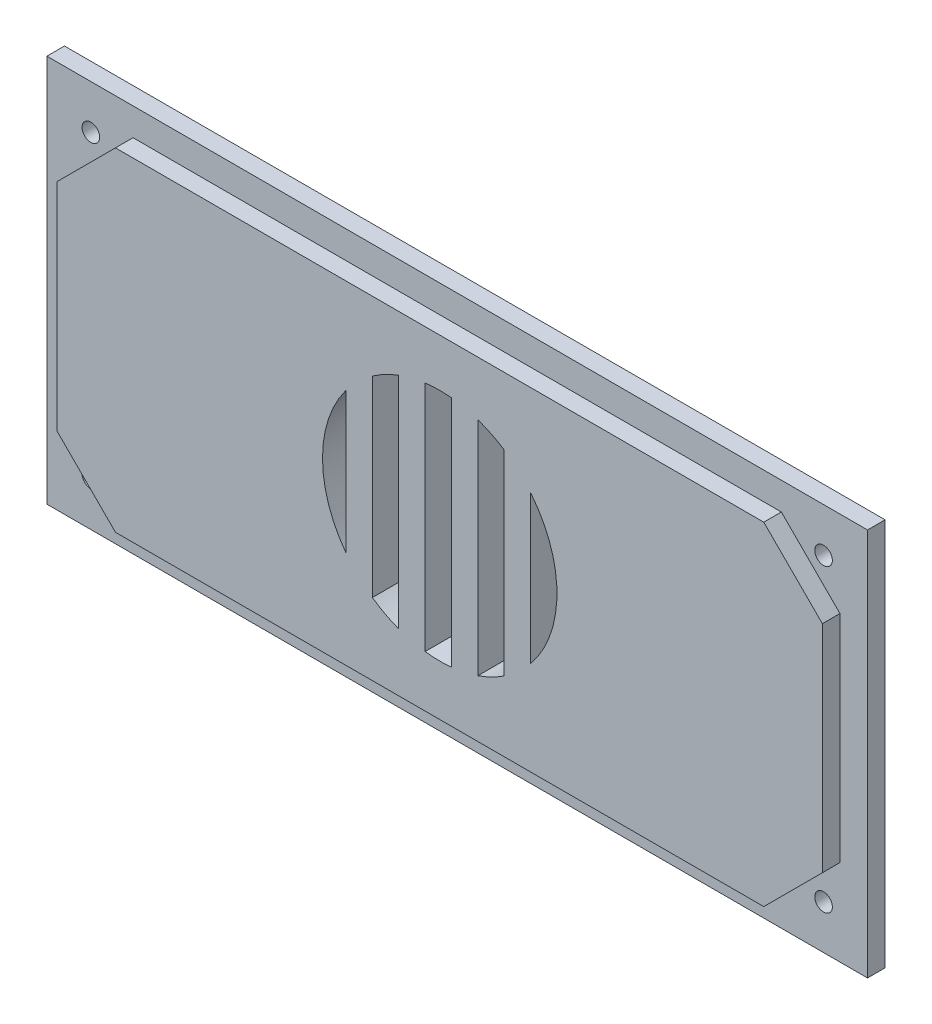
SolidWorks part; units mm, degrees
ref_plane "Front Plane" through (0, 0, 0) normal (0, 0, 1) x (1, 0, 0)
ref_plane "Top Plane" through (0, 0, 0) normal (0, 1, 0) x (1, 0, 0)
ref_plane "Right Plane" through (0, 0, 0) normal (1, 0, 0) x (0, 0, -1)
sketch "Sketch2" plane through (0, 0, 0) normal (0, 0, 1) x (1, 0, 0)
  line L1 (-70, 33.1) -> (70, 33.1)
  line L2 (-70, 33.1) -> (-70, -33.1)
  line L3 (-70, -33.1) -> (70, -33.1)
  line L4 (70, 33.1) -> (70, -33.1)
  line L5 (0, -33.1) -> (0, 33.1) construction
  line L6 (-70, 0) -> (70, 0) construction
  point P0 (0, 0)
  dimension "D1" = 140
  dimension "D2" = 66.2
extrude "Boss-Extrude1" add sketch "Sketch2" against normal blind 3
sketch "Sketch3" plane through (0, 0, 0) normal (0, 0, 1) x (1, 0, 0)
  line L1 (-65.3, 28.4) -> (65.3, 28.4)
  line L2 (-65.3, 28.4) -> (-65.3, -28.4)
  line L3 (-65.3, -28.4) -> (65.3, -28.4)
  line L4 (65.3, 28.4) -> (65.3, -28.4)
  line L5 (0, -28.4) -> (0, 28.4) construction
  line L6 (-65.3, 0) -> (65.3, 0) construction
  point P0 (0, 0)
  dimension "D1" = 130.6
  dimension "D2" = 56.8
extrude "Boss-Extrude2" add sketch "Sketch3" along normal blind 3
sketch "Sketch4" plane through (0, 0, -3) normal (0, 0, -1) x (-1, 0, 0)
  line L0 (-20.0198, 20.2318) -> (19.9802, 20.2318)
  line L1 (-20.0198, -19.7682) -> (19.9802, -19.7682)
  line L2 (-20.0198, 20.2318) -> (-20.0198, -19.7682)
  line L3 (19.9802, 20.2318) -> (19.9802, -19.7682)
  line L4 (-15.5198, 20.2318) -> (-15.5198, -19.7682)
  line L5 (-11.0198, 20.2318) -> (-11.0198, -19.7682)
  line L6 (-6.5198, 20.2318) -> (-6.5198, -19.7682)
  line L7 (-2.0198, 20.2318) -> (-2.0198, -19.7682)
  line L8 (2.4802, 20.2318) -> (2.4802, -19.7682)
  line L9 (6.9802, 20.2318) -> (6.9802, -19.7682)
  line L10 (11.4802, 20.2318) -> (11.4802, -19.7682)
  line L11 (15.9802, 20.2318) -> (15.9802, -19.7682)
  circle A0 centre (-0.0198, 0.2318) radius 20
  point P5 (-0.0198, 20.2318)
  point P8 (-0.0198, -19.7682)
  dimension "D1" = 40
extrude "Cut-Extrude1" cut sketch "Sketch4" against normal through all contours L4 A0 | L6 A0 L5 | L8 A0 L7 | L10 A0 L9 | A0 L11
sketch "Sketch5" plane through (0, 0, -3) normal (0, 0, -1) x (-1, 0, 0)
  line L0 (-70, -33.1) -> (-70, 33.1) construction
  line L1 (-62.5, 25.6) -> (62.5, 25.6) construction
  line L2 (-62.5, 25.6) -> (-62.5, -25.6) construction
  line L3 (-62.5, -25.6) -> (62.5, -25.6) construction
  line L4 (62.5, 25.6) -> (62.5, -25.6) construction
  line L5 (0, -25.6) -> (0, 25.6) construction
  line L6 (-62.5, 0) -> (62.5, 0) construction
  line L7 (-70, 33.1) -> (70, 33.1) construction
  circle A0 centre (-62.5, 25.6) radius 1.5
  circle A1 centre (62.5, 25.6) radius 1.5
  circle A2 centre (62.5, -25.6) radius 1.5
  circle A3 centre (-62.5, -25.6) radius 1.5
  point P8 (0, 0)
  dimension "D1" = 3
  dimension "D2" = 7.5
  dimension "D3" = 7.5
extrude "Cut-Extrude2" cut sketch "Sketch5" against normal through all
sketch "Sketch6" plane through (0, 0, 3) normal (0, 0, 1) x (1, 0, 0)
  line L0 (65.3, 28.4) -> (55.3, 28.4)
  line L1 (65.3, 28.4) -> (-65.3, 28.4) construction
  line L2 (55.3, 28.4) -> (65.3, 18.4)
  line L3 (65.3, -28.4) -> (65.3, 28.4) construction
  line L4 (65.3, 18.4) -> (65.3, 28.4)
  line L5 (65.3, -28.4) -> (65.3, -18.4)
  line L6 (65.3, -18.4) -> (55.3, -28.4)
  line L7 (-65.3, -28.4) -> (65.3, -28.4) construction
  line L8 (55.3, -28.4) -> (65.3, -28.4)
  line L9 (-65.3, -28.4) -> (-55.3, -28.4)
  line L10 (-55.3, -28.4) -> (-65.3, -18.4)
  line L11 (-65.3, 28.4) -> (-65.3, -28.4) construction
  line L12 (-65.3, -18.4) -> (-65.3, -28.4)
  line L13 (-65.3, 28.4) -> (-65.3, 18.4)
  line L14 (-65.3, 18.4) -> (-55.3, 28.4)
  line L15 (-55.3, 28.4) -> (-65.3, 28.4)
  dimension "D1" = 10
extrude "Cut-Extrude3" cut sketch "Sketch6" against normal up to surface (3 mm away) up to face at (0, 0, 0)
